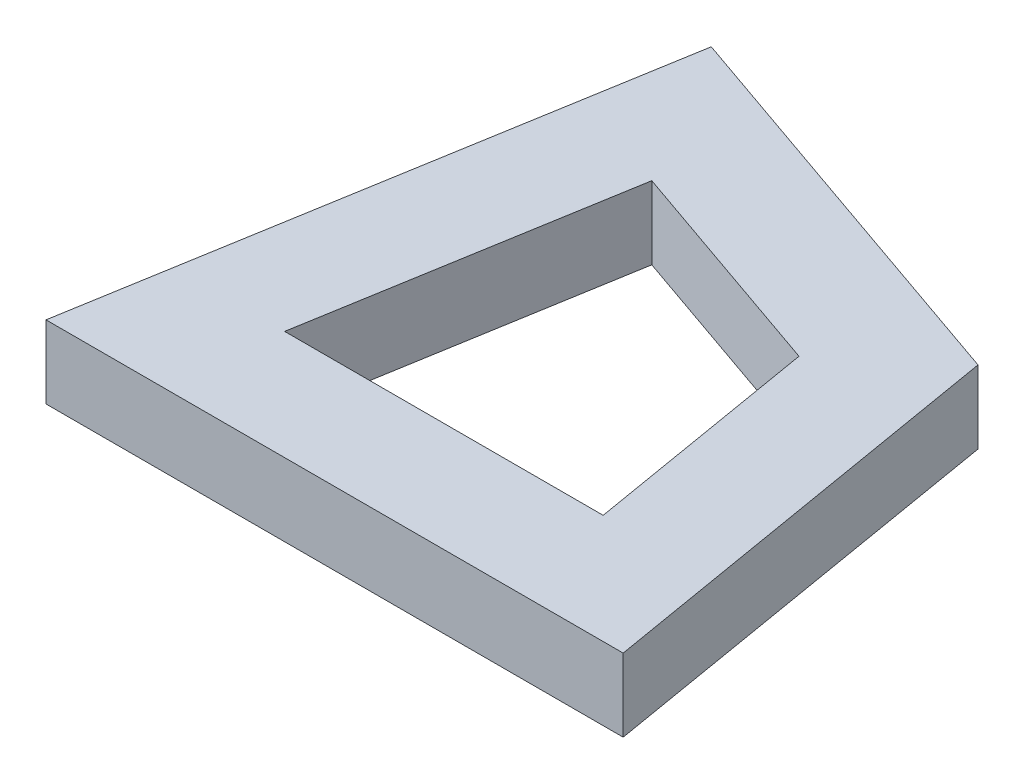
SolidWorks part; units mm, degrees
ref_plane "Front Plane" through (0, 0, 0) normal (0, 0, 1) x (1, 0, 0)
ref_plane "Top Plane" through (0, 0, 0) normal (0, 1, 0) x (1, 0, 0)
ref_plane "Right Plane" through (0, 0, 0) normal (1, 0, 0) x (0, 0, -1)
sketch "Sketch1" plane through (0, 0, 0) normal (0, 1, 0) x (1, 0, 0)
  line L0 (0, 0) -> (15.8408, 0)
  line L1 (15.8408, 0) -> (13.8609, 11.7183)
  line L2 (13.8609, 11.7183) -> (2.639, 15.6194)
  line L3 (2.639, 15.6194) -> (0, 0)
  line L4 (5.0059, 11.6205) -> (3.5494, 3)
  line L5 (3.5494, 3) -> (12.2914, 3)
  line L6 (12.2914, 3) -> (11.1986, 9.4677)
  line L7 (11.1986, 9.4677) -> (5.0059, 11.6205)
  point P4 (0, 0)
  point P10 (35.273, 13.2401)
  point P11 (27.7587, 61.9651)
  point P12 (35.2745, 13.2436)
  point P13 (30.6569, 10.5612)
  point P14 (35.2745, 13.2436)
  point P15 (32.8598, 27.5353)
  dimension "D1" = 15.8408
  dimension "D2" = 80.421
  dimension "D3" = 80.41
  dimension "D4" = 80.41
  dimension "D6" = 11.8844
  dimension "D7" = 11.8806
  dimension "D8" = 15.8408
  dimension "D5" = 3
extrude "Boss-Extrude1" add sketch "Sketch1" along normal blind 2
